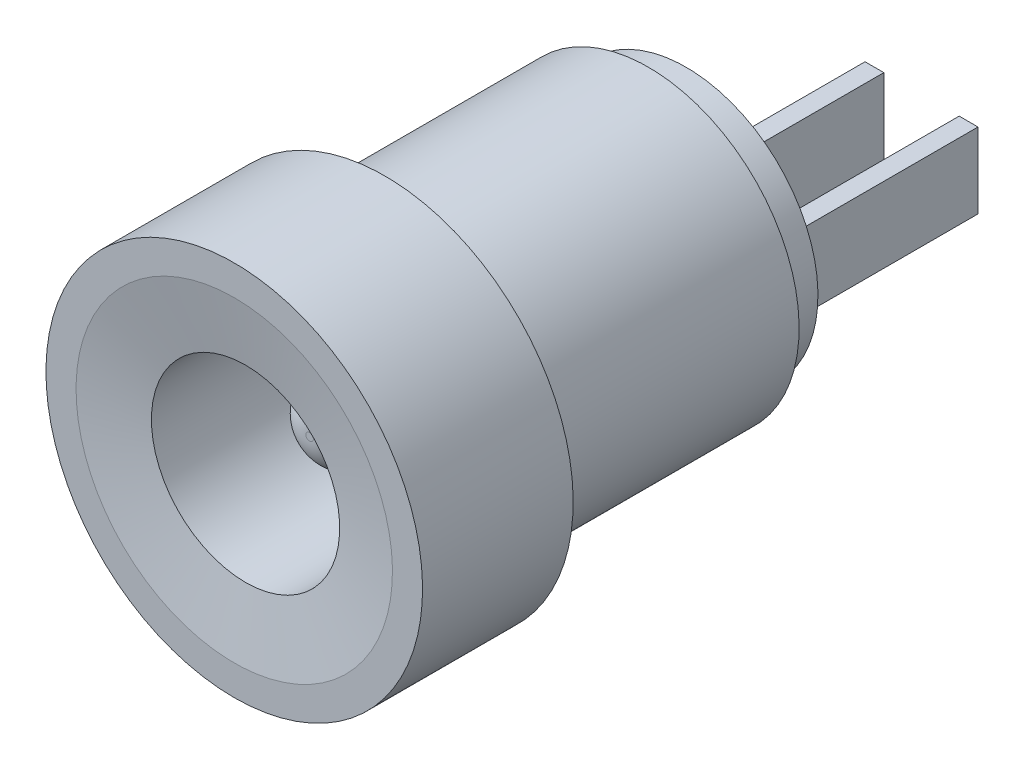
SolidWorks part; units mm, degrees
ref_plane "Płaszczyzna przednia" through (0, 0, 0) normal (0, 0, 1) x (1, 0, 0)
ref_plane "Płaszczyzna górna" through (0, 0, 0) normal (0, 1, 0) x (1, 0, 0)
ref_plane "Płaszczyzna prawa" through (0, 0, 0) normal (1, 0, 0) x (0, 0, -1)
sketch "Szkic1" plane through (0, 0, 0) normal (1, 0, 0) x (0, 0, -1)
  line L0 (2, 0) -> (12, 0)
  line L1 (12, 0) -> (12, 3.5)
  line L2 (12, 3.5) -> (11, 3.5)
  line L3 (11, 3.5) -> (11, 4)
  line L4 (11, 4) -> (4, 4)
  line L5 (4, 4) -> (4, 5)
  line L6 (4, 5) -> (0, 5)
  line L7 (0, 5) -> (0, 2.5)
  line L8 (0, 2.5) -> (8, 2.5)
  line L9 (8, 2.5) -> (8, 1.1)
  line L10 (8, 1.1) -> (2, 1.1)
  line L11 (2, 1.1) -> (2, 0)
  line L12 (-23.6978, 0) -> (32.9427, 0) construction
  point P3 (-1.6075, 4)
  dimension "D1" = 1.1
  dimension "D2" = 4
  dimension "D3" = 5
  dimension "D4" = 2.5
  dimension "D5" = 2
  dimension "D6" = 8
  dimension "D7" = 3.5
  dimension "D8" = 4
  dimension "D9" = 8
  dimension "D10" = 1
revolve "Obrót1" add sketch "Szkic1" angle 360 about L12
fillet "Zaokrąglenie1" radius 1 1 edges at (0, -1.1, -2)
chamfer "Sfazowanie1" distance 0.3 angle 80 1 edges at (0, -2.5, 0)
sketch "Szkic2" plane through (0, 0, -12) normal (0, 0, -1) x (-1, 0, 0)
  line L0 (-0.25, -1) -> (0.25, 1) construction
  line L1 (-2.75, 1) -> (-2.25, 1)
  line L2 (-2.75, 1) -> (-2.75, -1)
  line L3 (-2.75, -1) -> (-2.25, -1)
  line L4 (-2.25, 1) -> (-2.25, -1)
  line L5 (-0.25, 1) -> (0.25, 1)
  line L6 (-0.25, 1) -> (-0.25, -1)
  line L7 (-0.25, -1) -> (0.25, -1)
  line L8 (0.25, 1) -> (0.25, -1)
  point P8 (0, 0)
  point P9 (-0.4873, -1.2399)
  dimension "D1" = 0.5
  dimension "D2" = 2
  dimension "D3" = 2
extrude "Dodanie-wyciągnięcie1" add sketch "Szkic2" along normal blind 5
